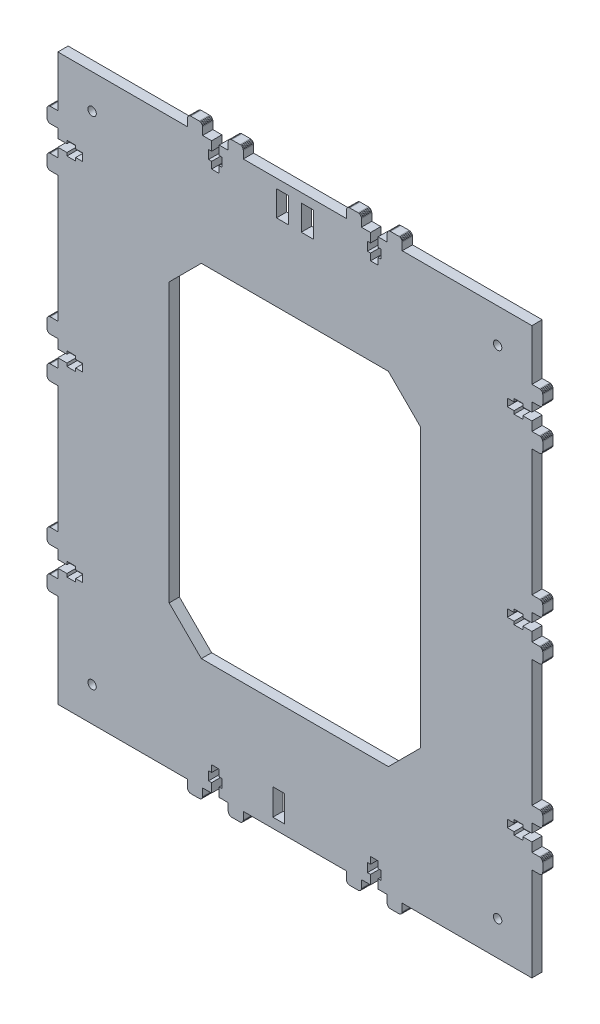
SolidWorks part; units mm, degrees
ref_plane "Plano frontal" through (0, 0, 0) normal (0, 0, 1) x (1, 0, 0)
ref_plane "Plano superior" through (0, 0, 0) normal (0, 1, 0) x (1, 0, 0)
ref_plane "Plano direito" through (0, 0, 0) normal (1, 0, 0) x (0, 0, -1)
sketch "Model" plane through (0, 0, 0) normal (0, 0, 1) x (1, 0, 0)
  line L0 (136.5926, 337.8518) -> (136.5926, 343.1518)
  line L1 (136.5926, 332.7518) -> (138.3926, 332.7518)
  line L2 (138.3926, 337.8518) -> (136.5926, 337.8518)
  line L3 (130.3926, 337.8518) -> (130.3926, 332.7518)
  line L4 (234.6925, 13.2519) -> (229.3925, 13.2519)
  line L5 (132.1926, 332.7518) -> (132.1926, 328.8018)
  line L6 (319.1925, 280.8519) -> (319.1925, 207.0019)
  line L7 (47.6926, 82.0519) -> (47.6926, 80.2519)
  line L8 (56.7426, 86.4519) -> (52.7926, 86.4519)
  line L9 (52.7926, 80.2519) -> (52.7926, 82.0519)
  line L10 (42.3926, 91.7519) -> (38.0426, 91.7519)
  line L11 (42.3926, 67.9519) -> (38.0426, 67.9519)
  line L12 (52.7926, 88.2519) -> (47.6926, 88.2519)
  line L13 (56.7426, 82.0519) -> (56.7426, 86.4519)
  line L14 (229.3925, 337.8518) -> (229.3925, 343.1518)
  line L15 (319.1925, 174.4019) -> (319.1925, 100.5519)
  line L16 (224.9925, 343.1518) -> (224.9925, 337.8518)
  line L17 (52.7926, 299.3519) -> (52.7926, 301.1519)
  line L18 (229.3925, 332.7518) -> (231.1925, 332.7518)
  line L19 (132.1926, 343.1518) -> (132.1926, 337.8518)
  line L20 (56.7426, 294.9519) -> (56.7426, 299.3519)
  line L21 (223.1925, 337.8518) -> (223.1925, 332.7518)
  line L22 (47.6926, 88.2519) -> (47.6926, 86.4519)
  line L23 (47.6926, 80.2519) -> (52.7926, 80.2519)
  line L24 (42.3926, 13.2519) -> (42.3926, 67.9519)
  line L25 (52.7926, 293.1519) -> (52.7926, 294.9519)
  line L26 (319.1925, 13.2519) -> (243.4925, 13.2519)
  line L27 (52.7926, 188.5019) -> (56.7426, 188.5019)
  line L28 (56.7426, 192.9019) -> (52.7926, 192.9019)
  line L29 (313.8925, 301.1519) -> (308.7925, 301.1519)
  line L30 (313.8925, 299.3519) -> (313.8925, 301.1519)
  line L31 (304.8425, 294.9519) -> (308.7925, 294.9519)
  line L32 (47.6926, 293.1519) -> (52.7926, 293.1519)
  line L33 (138.3926, 18.5519) -> (138.3926, 23.6519)
  line L34 (136.5926, 18.5519) -> (138.3926, 18.5519)
  line L35 (132.1926, 27.6019) -> (132.1926, 23.6519)
  line L36 (138.3926, 23.6519) -> (136.5926, 23.6519)
  line L37 (126.8926, 13.2519) -> (126.8926, 8.902)
  line L38 (150.6926, 13.2519) -> (150.6926, 8.902)
  line L39 (130.3926, 23.6519) -> (130.3926, 18.5519)
  line L40 (42.3926, 198.2019) -> (38.0426, 198.2019)
  line L41 (319.1925, 67.9519) -> (319.1925, 13.2519)
  line L42 (132.1926, 18.5519) -> (132.1926, 13.2519)
  line L43 (132.1926, 23.6519) -> (130.3926, 23.6519)
  line L44 (130.3926, 18.5519) -> (132.1926, 18.5519)
  line L45 (42.3926, 313.4519) -> (42.3926, 343.1518)
  line L46 (42.3926, 188.5019) -> (47.6926, 188.5019)
  line L47 (47.6926, 192.9019) -> (42.3926, 192.9019)
  line L48 (47.6926, 186.7019) -> (52.7926, 186.7019)
  line L49 (231.1925, 18.5519) -> (231.1925, 23.6519)
  line L50 (229.3925, 18.5519) -> (231.1925, 18.5519)
  line L51 (224.9925, 27.6019) -> (224.9925, 23.6519)
  line L52 (308.7925, 301.1519) -> (308.7925, 299.3519)
  line L53 (319.1925, 289.6519) -> (323.5425, 289.6519)
  line L54 (319.1925, 313.4518) -> (323.5425, 313.4518)
  line L55 (308.7925, 293.1519) -> (313.8925, 293.1519)
  line L56 (304.8425, 299.3519) -> (304.8425, 294.9519)
  line L57 (304.8425, 82.0519) -> (308.7925, 82.0519)
  line L58 (304.8425, 192.9019) -> (304.8425, 188.5019)
  line L59 (118.0926, 13.2519) -> (42.3926, 13.2519)
  line L60 (319.1925, 192.9019) -> (313.8925, 192.9019)
  line L61 (319.1925, 294.9519) -> (319.1925, 289.6519)
  line L62 (319.1925, 304.6519) -> (319.1925, 299.3519)
  line L63 (308.7925, 294.9519) -> (308.7925, 293.1519)
  line L64 (313.8925, 293.1519) -> (313.8925, 294.9519)
  line L65 (308.7925, 192.9019) -> (304.8425, 192.9019)
  line L66 (319.1925, 198.2019) -> (319.1925, 192.9019)
  line L67 (231.1925, 337.8518) -> (229.3925, 337.8518)
  line L68 (313.8925, 82.0519) -> (319.1925, 82.0519)
  line L69 (308.7925, 82.0519) -> (308.7925, 80.2519)
  line L70 (210.8925, 343.1518) -> (210.8925, 347.5018)
  line L71 (231.1925, 332.7518) -> (231.1925, 337.8518)
  line L72 (224.9925, 337.8518) -> (223.1925, 337.8518)
  line L73 (47.6926, 86.4519) -> (42.3926, 86.4519)
  line L74 (52.7926, 86.4519) -> (52.7926, 88.2519)
  line L75 (319.1925, 76.7519) -> (323.5425, 76.7519)
  line L76 (319.1925, 100.5519) -> (323.5425, 100.5519)
  line L77 (308.7925, 80.2519) -> (313.8925, 80.2519)
  line L78 (52.7926, 301.1519) -> (47.6926, 301.1519)
  line L79 (229.3925, 13.2519) -> (229.3925, 18.5519)
  line L80 (42.3926, 192.9019) -> (42.3926, 198.2019)
  line L81 (52.7926, 186.7019) -> (52.7926, 188.5019)
  line L82 (47.6926, 188.5019) -> (47.6926, 186.7019)
  line L83 (42.3926, 82.0519) -> (47.6926, 82.0519)
  line L84 (52.7926, 82.0519) -> (56.7426, 82.0519)
  line L85 (313.8925, 188.5019) -> (319.1925, 188.5019)
  line L86 (308.7925, 188.5019) -> (308.7925, 186.7019)
  line L87 (313.8925, 186.7019) -> (313.8925, 188.5019)
  line L88 (313.8925, 194.7019) -> (308.7925, 194.7019)
  line L89 (132.1926, 13.2519) -> (126.8926, 13.2519)
  line L90 (224.9925, 13.2519) -> (219.6925, 13.2519)
  line L91 (47.6926, 294.9519) -> (47.6926, 293.1519)
  line L92 (231.1925, 23.6519) -> (229.3925, 23.6519)
  line L93 (136.5926, 13.2519) -> (136.5926, 18.5519)
  line L94 (136.5926, 23.6519) -> (136.5926, 27.6019)
  line L95 (141.8926, 13.2519) -> (136.5926, 13.2519)
  line L96 (56.7426, 188.5019) -> (56.7426, 192.9019)
  line L97 (47.6926, 194.7019) -> (47.6926, 192.9019)
  line L98 (52.7926, 194.7019) -> (47.6926, 194.7019)
  line L99 (319.1925, 82.0519) -> (319.1925, 76.7519)
  line L100 (313.8925, 88.2519) -> (308.7925, 88.2519)
  line L101 (132.1926, 337.8518) -> (130.3926, 337.8518)
  line L102 (136.5926, 328.8018) -> (136.5926, 332.7518)
  line L103 (130.3926, 332.7518) -> (132.1926, 332.7518)
  line L104 (141.8926, 343.1518) -> (141.8926, 347.5018)
  line L105 (229.3925, 343.1518) -> (234.6925, 343.1518)
  line L106 (136.5926, 27.6019) -> (132.1926, 27.6019)
  line L107 (42.3926, 294.9519) -> (47.6926, 294.9519)
  line L108 (52.7926, 294.9519) -> (56.7426, 294.9519)
  line L109 (56.7426, 299.3519) -> (52.7926, 299.3519)
  line L110 (42.3926, 86.4519) -> (42.3926, 91.7519)
  line L111 (42.3926, 100.5519) -> (42.3926, 174.4019)
  line L112 (42.3926, 207.0019) -> (42.3926, 280.8519)
  line L113 (42.3926, 76.7519) -> (42.3926, 82.0519)
  line L114 (223.1925, 23.6519) -> (223.1925, 18.5519)
  line L115 (229.3925, 27.6019) -> (224.9925, 27.6019)
  line L116 (224.9925, 18.5519) -> (224.9925, 13.2519)
  line L117 (304.8425, 188.5019) -> (308.7925, 188.5019)
  line L118 (308.7925, 194.7019) -> (308.7925, 192.9019)
  line L119 (319.1925, 183.2019) -> (323.5425, 183.2019)
  line L120 (319.1925, 207.0019) -> (323.5425, 207.0019)
  line L121 (308.7925, 186.7019) -> (313.8925, 186.7019)
  line L122 (138.3926, 332.7518) -> (138.3926, 337.8518)
  line L123 (132.1926, 328.8018) -> (136.5926, 328.8018)
  line L124 (219.6925, 13.2519) -> (219.6925, 8.902)
  line L125 (243.4925, 13.2519) -> (243.4925, 8.902)
  line L126 (229.3925, 328.8018) -> (229.3925, 332.7518)
  line L127 (234.6925, 343.1518) -> (234.6925, 347.5018)
  line L128 (42.3926, 183.2019) -> (42.3926, 188.5019)
  line L129 (319.1925, 299.3519) -> (313.8925, 299.3519)
  line L130 (308.7925, 299.3519) -> (304.8425, 299.3519)
  line L131 (319.1925, 188.5019) -> (319.1925, 183.2019)
  line L132 (313.8925, 294.9519) -> (319.1925, 294.9519)
  line L133 (52.7926, 192.9019) -> (52.7926, 194.7019)
  line L134 (319.1925, 91.7519) -> (319.1925, 86.4519)
  line L135 (229.3925, 23.6519) -> (229.3925, 27.6019)
  line L136 (136.5926, 343.1518) -> (141.8926, 343.1518)
  line L137 (150.6926, 343.1518) -> (210.8925, 343.1518)
  line L138 (219.6925, 343.1518) -> (224.9925, 343.1518)
  line L139 (42.3926, 174.4019) -> (38.0426, 174.4019)
  line L140 (223.1925, 18.5519) -> (224.9925, 18.5519)
  line L141 (47.6926, 301.1519) -> (47.6926, 299.3519)
  line L142 (47.6926, 299.3519) -> (42.3926, 299.3519)
  line L143 (42.3926, 299.3519) -> (42.3926, 304.6519)
  line L144 (210.8925, 13.2519) -> (150.6926, 13.2519)
  line L145 (42.3926, 304.6519) -> (38.0426, 304.6519)
  line L146 (243.4925, 343.1518) -> (319.1925, 343.1518)
  line L147 (319.1925, 343.1518) -> (319.1925, 313.4518)
  line L148 (223.1925, 332.7518) -> (224.9925, 332.7518)
  line L149 (224.9925, 332.7518) -> (224.9925, 328.8018)
  line L150 (224.9925, 328.8018) -> (229.3925, 328.8018)
  line L151 (319.1925, 86.4519) -> (313.8925, 86.4519)
  line L152 (313.8925, 86.4519) -> (313.8925, 88.2519)
  line L153 (308.7925, 88.2519) -> (308.7925, 86.4519)
  line L154 (308.7925, 86.4519) -> (304.8425, 86.4519)
  line L155 (304.8425, 86.4519) -> (304.8425, 82.0519)
  line L156 (224.9925, 23.6519) -> (223.1925, 23.6519)
  line L157 (42.3926, 343.1518) -> (118.0926, 343.1518)
  line L158 (118.0926, 343.1518) -> (118.0926, 347.5018)
  line L159 (124.8926, 349.5018) -> (125.4102, 349.4337)
  line L160 (125.4102, 349.4337) -> (125.8926, 349.2339)
  line L161 (125.8926, 349.2339) -> (126.3068, 348.9161)
  line L162 (126.3068, 348.9161) -> (126.6246, 348.5018)
  line L163 (126.6246, 348.5018) -> (126.8244, 348.0195)
  line L164 (126.8926, 347.5018) -> (126.8926, 343.1518)
  line L165 (126.8244, 348.0195) -> (126.8926, 347.5018)
  line L166 (141.8926, 347.5018) -> (141.9607, 348.0195)
  line L167 (141.9607, 348.0195) -> (142.1605, 348.5018)
  line L168 (142.1605, 348.5018) -> (142.4783, 348.9161)
  line L169 (142.4783, 348.9161) -> (142.8926, 349.2339)
  line L170 (142.8926, 349.2339) -> (143.3749, 349.4337)
  line L171 (143.8926, 349.5018) -> (148.6926, 349.5018)
  line L172 (143.3749, 349.4337) -> (143.8926, 349.5018)
  line L173 (150.6926, 347.5018) -> (150.6926, 343.1518)
  line L174 (150.6926, 347.5018) -> (150.6244, 348.0195)
  line L175 (150.6244, 348.0195) -> (150.4246, 348.5018)
  line L176 (150.4246, 348.5018) -> (150.1068, 348.9161)
  line L177 (150.1068, 348.9161) -> (149.6926, 349.2339)
  line L178 (149.6926, 349.2339) -> (149.2102, 349.4337)
  line L179 (149.2102, 349.4337) -> (148.6926, 349.5018)
  line L180 (118.0926, 347.5018) -> (118.1607, 348.0195)
  line L181 (118.1607, 348.0195) -> (118.3605, 348.5018)
  line L182 (118.3605, 348.5018) -> (118.6784, 348.9161)
  line L183 (118.6784, 348.9161) -> (119.0926, 349.2339)
  line L184 (119.0926, 349.2339) -> (119.5749, 349.4337)
  line L185 (120.0926, 349.5018) -> (124.8926, 349.5018)
  line L186 (119.5749, 349.4337) -> (120.0926, 349.5018)
  line L187 (234.6925, 347.5018) -> (234.7607, 348.0195)
  line L188 (234.7607, 348.0195) -> (234.9605, 348.5018)
  line L189 (234.9605, 348.5018) -> (235.2783, 348.9161)
  line L190 (235.2783, 348.9161) -> (235.6925, 349.2339)
  line L191 (235.6925, 349.2339) -> (236.1749, 349.4337)
  line L192 (236.6925, 349.5018) -> (241.4925, 349.5018)
  line L193 (236.1749, 349.4337) -> (236.6925, 349.5018)
  line L194 (243.4925, 347.5018) -> (243.4925, 343.1518)
  line L195 (243.4925, 347.5018) -> (243.4244, 348.0195)
  line L196 (243.4244, 348.0195) -> (243.2246, 348.5018)
  line L197 (243.2246, 348.5018) -> (242.9067, 348.9161)
  line L198 (242.9067, 348.9161) -> (242.4925, 349.2339)
  line L199 (242.4925, 349.2339) -> (242.0102, 349.4337)
  line L200 (242.0102, 349.4337) -> (241.4925, 349.5018)
  line L201 (219.6925, 347.5018) -> (219.6925, 343.1518)
  line L202 (219.6925, 347.5018) -> (219.6244, 348.0195)
  line L203 (219.6244, 348.0195) -> (219.4246, 348.5018)
  line L204 (219.4246, 348.5018) -> (219.1068, 348.9161)
  line L205 (219.1068, 348.9161) -> (218.6925, 349.2339)
  line L206 (218.6925, 349.2339) -> (218.2102, 349.4337)
  line L207 (218.2102, 349.4337) -> (217.6925, 349.5018)
  line L208 (210.8925, 347.5018) -> (210.9607, 348.0195)
  line L209 (210.9607, 348.0195) -> (211.1605, 348.5018)
  line L210 (211.1605, 348.5018) -> (211.4783, 348.9161)
  line L211 (211.4783, 348.9161) -> (211.8925, 349.2339)
  line L212 (211.8925, 349.2339) -> (212.3749, 349.4337)
  line L213 (212.8925, 349.5018) -> (217.6925, 349.5018)
  line L214 (212.3749, 349.4337) -> (212.8925, 349.5018)
  line L215 (210.8925, 8.902) -> (210.8925, 13.2519)
  line L216 (210.8925, 8.902) -> (210.9607, 8.3843)
  line L217 (210.9607, 8.3843) -> (211.1605, 7.902)
  line L218 (211.1605, 7.902) -> (211.4783, 7.4877)
  line L219 (211.4783, 7.4877) -> (211.8925, 7.1699)
  line L220 (211.8925, 7.1699) -> (212.3749, 6.9701)
  line L221 (212.3749, 6.9701) -> (212.8925, 6.902)
  line L222 (219.6925, 8.902) -> (219.6244, 8.3843)
  line L223 (219.6244, 8.3843) -> (219.4246, 7.902)
  line L224 (219.4246, 7.902) -> (219.1067, 7.4877)
  line L225 (219.1067, 7.4877) -> (218.6925, 7.1699)
  line L226 (218.6925, 7.1699) -> (218.2102, 6.9701)
  line L227 (217.6925, 6.902) -> (212.8925, 6.902)
  line L228 (218.2102, 6.9701) -> (217.6925, 6.902)
  line L229 (323.5425, 174.4019) -> (319.1925, 174.4019)
  line L230 (323.5425, 174.4019) -> (324.0601, 174.47)
  line L231 (324.0601, 174.47) -> (324.5425, 174.6698)
  line L232 (324.5425, 174.6698) -> (324.9567, 174.9877)
  line L233 (324.9567, 174.9877) -> (325.2746, 175.4019)
  line L234 (325.2746, 175.4019) -> (325.4744, 175.8843)
  line L235 (325.4744, 175.8843) -> (325.5425, 176.4019)
  line L236 (325.5425, 93.7519) -> (325.4744, 93.2343)
  line L237 (325.4744, 93.2343) -> (325.2746, 92.7519)
  line L238 (325.2746, 92.7519) -> (324.9567, 92.3377)
  line L239 (324.9567, 92.3377) -> (324.5425, 92.0199)
  line L240 (324.5425, 92.0199) -> (324.0601, 91.8201)
  line L241 (323.5425, 91.7519) -> (319.1925, 91.7519)
  line L242 (324.0601, 91.8201) -> (323.5425, 91.7519)
  line L243 (36.0426, 93.7519) -> (36.0426, 98.5519)
  line L244 (36.0426, 93.7519) -> (36.1107, 93.2343)
  line L245 (36.1107, 93.2343) -> (36.3105, 92.7519)
  line L246 (36.3105, 92.7519) -> (36.6284, 92.3377)
  line L247 (36.6284, 92.3377) -> (37.0426, 92.0199)
  line L248 (37.0426, 92.0199) -> (37.525, 91.8201)
  line L249 (37.525, 91.8201) -> (38.0426, 91.7519)
  line L250 (38.0426, 67.9519) -> (37.525, 68.0201)
  line L251 (37.525, 68.0201) -> (37.0426, 68.2199)
  line L252 (37.0426, 68.2199) -> (36.6284, 68.5377)
  line L253 (36.6284, 68.5377) -> (36.3105, 68.9519)
  line L254 (36.3105, 68.9519) -> (36.1107, 69.4343)
  line L255 (36.0426, 69.9519) -> (36.0426, 74.7519)
  line L256 (36.1107, 69.4343) -> (36.0426, 69.9519)
  line L257 (38.0426, 76.7519) -> (42.3926, 76.7519)
  line L258 (38.0426, 76.7519) -> (37.525, 76.6838)
  line L259 (37.525, 76.6838) -> (37.0426, 76.484)
  line L260 (37.0426, 76.484) -> (36.6284, 76.1661)
  line L261 (36.6284, 76.1661) -> (36.3105, 75.7519)
  line L262 (36.3105, 75.7519) -> (36.1107, 75.2696)
  line L263 (36.1107, 75.2696) -> (36.0426, 74.7519)
  line L264 (36.0426, 306.6519) -> (36.0426, 311.4519)
  line L265 (36.0426, 306.6519) -> (36.1107, 306.1342)
  line L266 (36.1107, 306.1342) -> (36.3105, 305.6519)
  line L267 (36.3105, 305.6519) -> (36.6284, 305.2376)
  line L268 (36.6284, 305.2376) -> (37.0426, 304.9198)
  line L269 (37.0426, 304.9198) -> (37.525, 304.72)
  line L270 (37.525, 304.72) -> (38.0426, 304.6519)
  line L271 (325.5425, 69.9519) -> (325.4744, 69.4343)
  line L272 (325.4744, 69.4343) -> (325.2746, 68.9519)
  line L273 (325.2746, 68.9519) -> (324.9567, 68.5377)
  line L274 (324.9567, 68.5377) -> (324.5425, 68.2199)
  line L275 (324.5425, 68.2199) -> (324.0601, 68.0201)
  line L276 (323.5425, 67.9519) -> (319.1925, 67.9519)
  line L277 (324.0601, 68.0201) -> (323.5425, 67.9519)
  line L278 (124.8926, 6.902) -> (120.0926, 6.902)
  line L279 (124.8926, 6.902) -> (125.4102, 6.9701)
  line L280 (125.4102, 6.9701) -> (125.8926, 7.1699)
  line L281 (125.8926, 7.1699) -> (126.3068, 7.4877)
  line L282 (126.3068, 7.4877) -> (126.6246, 7.902)
  line L283 (126.6246, 7.902) -> (126.8244, 8.3843)
  line L284 (126.8244, 8.3843) -> (126.8926, 8.902)
  line L285 (118.0926, 8.902) -> (118.0926, 13.2519)
  line L286 (118.0926, 8.902) -> (118.1607, 8.3843)
  line L287 (118.1607, 8.3843) -> (118.3605, 7.902)
  line L288 (118.3605, 7.902) -> (118.6784, 7.4877)
  line L289 (118.6784, 7.4877) -> (119.0926, 7.1699)
  line L290 (119.0926, 7.1699) -> (119.5749, 6.9701)
  line L291 (119.5749, 6.9701) -> (120.0926, 6.902)
  line L292 (38.0426, 100.5519) -> (42.3926, 100.5519)
  line L293 (38.0426, 100.5519) -> (37.525, 100.4838)
  line L294 (37.525, 100.4838) -> (37.0426, 100.284)
  line L295 (37.0426, 100.284) -> (36.6284, 99.9661)
  line L296 (36.6284, 99.9661) -> (36.3105, 99.5519)
  line L297 (36.3105, 99.5519) -> (36.1107, 99.0696)
  line L298 (36.1107, 99.0696) -> (36.0426, 98.5519)
  line L299 (323.5425, 304.6519) -> (319.1925, 304.6519)
  line L300 (323.5425, 304.6519) -> (324.0601, 304.72)
  line L301 (324.0601, 304.72) -> (324.5425, 304.9198)
  line L302 (324.5425, 304.9198) -> (324.9567, 305.2376)
  line L303 (324.9567, 305.2376) -> (325.2746, 305.6519)
  line L304 (325.2746, 305.6519) -> (325.4744, 306.1342)
  line L305 (325.4744, 306.1342) -> (325.5425, 306.6519)
  line L306 (325.5425, 287.6519) -> (325.5425, 282.8519)
  line L307 (325.5425, 287.6519) -> (325.4744, 288.1695)
  line L308 (325.4744, 288.1695) -> (325.2746, 288.6519)
  line L309 (325.2746, 288.6519) -> (324.9567, 289.0661)
  line L310 (324.9567, 289.0661) -> (324.5425, 289.3839)
  line L311 (324.5425, 289.3839) -> (324.0601, 289.5837)
  line L312 (324.0601, 289.5837) -> (323.5425, 289.6519)
  line L313 (323.5425, 280.8519) -> (319.1925, 280.8519)
  line L314 (323.5425, 280.8519) -> (324.0601, 280.92)
  line L315 (324.0601, 280.92) -> (324.5425, 281.1198)
  line L316 (324.5425, 281.1198) -> (324.9567, 281.4377)
  line L317 (324.9567, 281.4377) -> (325.2746, 281.8519)
  line L318 (325.2746, 281.8519) -> (325.4744, 282.3342)
  line L319 (325.4744, 282.3342) -> (325.5425, 282.8519)
  line L320 (148.6926, 6.902) -> (143.8926, 6.902)
  line L321 (148.6926, 6.902) -> (149.2102, 6.9701)
  line L322 (149.2102, 6.9701) -> (149.6926, 7.1699)
  line L323 (149.6926, 7.1699) -> (150.1068, 7.4877)
  line L324 (150.1068, 7.4877) -> (150.4246, 7.902)
  line L325 (150.4246, 7.902) -> (150.6244, 8.3843)
  line L326 (150.6244, 8.3843) -> (150.6926, 8.902)
  line L327 (36.0426, 200.2019) -> (36.0426, 205.0019)
  line L328 (36.0426, 200.2019) -> (36.1107, 199.6843)
  line L329 (36.1107, 199.6843) -> (36.3105, 199.2019)
  line L330 (36.3105, 199.2019) -> (36.6284, 198.7877)
  line L331 (36.6284, 198.7877) -> (37.0426, 198.4698)
  line L332 (37.0426, 198.4698) -> (37.525, 198.27)
  line L333 (37.525, 198.27) -> (38.0426, 198.2019)
  line L334 (141.8926, 8.902) -> (141.8926, 13.2519)
  line L335 (141.8926, 8.902) -> (141.9607, 8.3843)
  line L336 (141.9607, 8.3843) -> (142.1605, 7.902)
  line L337 (142.1605, 7.902) -> (142.4783, 7.4877)
  line L338 (142.4783, 7.4877) -> (142.8926, 7.1699)
  line L339 (142.8926, 7.1699) -> (143.3749, 6.9701)
  line L340 (143.3749, 6.9701) -> (143.8926, 6.902)
  line L341 (38.0426, 207.0019) -> (42.3926, 207.0019)
  line L342 (38.0426, 207.0019) -> (37.525, 206.9337)
  line L343 (37.525, 206.9337) -> (37.0426, 206.7339)
  line L344 (37.0426, 206.7339) -> (36.6284, 206.4161)
  line L345 (36.6284, 206.4161) -> (36.3105, 206.0019)
  line L346 (36.3105, 206.0019) -> (36.1107, 205.5195)
  line L347 (36.1107, 205.5195) -> (36.0426, 205.0019)
  line L348 (38.0426, 313.4519) -> (42.3926, 313.4519)
  line L349 (38.0426, 313.4519) -> (37.525, 313.3837)
  line L350 (37.525, 313.3837) -> (37.0426, 313.1839)
  line L351 (37.0426, 313.1839) -> (36.6284, 312.8661)
  line L352 (36.6284, 312.8661) -> (36.3105, 312.4519)
  line L353 (36.3105, 312.4519) -> (36.1107, 311.9695)
  line L354 (36.1107, 311.9695) -> (36.0426, 311.4519)
  line L355 (38.0426, 289.6519) -> (42.3926, 289.6519)
  line L356 (38.0426, 289.6519) -> (37.525, 289.5837)
  line L357 (37.525, 289.5837) -> (37.0426, 289.3839)
  line L358 (37.0426, 289.3839) -> (36.6284, 289.0661)
  line L359 (36.6284, 289.0661) -> (36.3105, 288.6519)
  line L360 (36.3105, 288.6519) -> (36.1107, 288.1695)
  line L361 (36.1107, 288.1695) -> (36.0426, 287.6519)
  line L362 (323.5425, 313.4518) -> (324.0601, 313.3837)
  line L363 (324.0601, 313.3837) -> (324.5425, 313.1839)
  line L364 (324.5425, 313.1839) -> (324.9567, 312.8661)
  line L365 (324.9567, 312.8661) -> (325.2746, 312.4518)
  line L366 (325.2746, 312.4518) -> (325.4744, 311.9695)
  line L367 (325.5425, 311.4518) -> (325.5425, 306.6519)
  line L368 (325.4744, 311.9695) -> (325.5425, 311.4518)
  line L369 (236.6925, 6.902) -> (236.1749, 6.9701)
  line L370 (236.1749, 6.9701) -> (235.6925, 7.1699)
  line L371 (235.6925, 7.1699) -> (235.2783, 7.4877)
  line L372 (235.2783, 7.4877) -> (234.9605, 7.902)
  line L373 (234.9605, 7.902) -> (234.7607, 8.3843)
  line L374 (234.6925, 8.902) -> (234.6925, 13.2519)
  line L375 (234.7607, 8.3843) -> (234.6925, 8.902)
  line L376 (325.5425, 74.7519) -> (325.5425, 69.9519)
  line L377 (325.5425, 74.7519) -> (325.4744, 75.2696)
  line L378 (325.4744, 75.2696) -> (325.2746, 75.7519)
  line L379 (325.2746, 75.7519) -> (324.9567, 76.1661)
  line L380 (324.9567, 76.1661) -> (324.5425, 76.484)
  line L381 (324.5425, 76.484) -> (324.0601, 76.6838)
  line L382 (324.0601, 76.6838) -> (323.5425, 76.7519)
  line L383 (323.5425, 100.5519) -> (324.0601, 100.4838)
  line L384 (324.0601, 100.4838) -> (324.5425, 100.284)
  line L385 (324.5425, 100.284) -> (324.9567, 99.9661)
  line L386 (324.9567, 99.9661) -> (325.2746, 99.5519)
  line L387 (325.2746, 99.5519) -> (325.4744, 99.0696)
  line L388 (325.5425, 98.5519) -> (325.5425, 93.7519)
  line L389 (325.4744, 99.0696) -> (325.5425, 98.5519)
  line L390 (325.5425, 200.2019) -> (325.4744, 199.6842)
  line L391 (325.4744, 199.6842) -> (325.2746, 199.2019)
  line L392 (325.2746, 199.2019) -> (324.9567, 198.7877)
  line L393 (324.9567, 198.7877) -> (324.5425, 198.4698)
  line L394 (324.5425, 198.4698) -> (324.0601, 198.27)
  line L395 (323.5425, 198.2019) -> (319.1925, 198.2019)
  line L396 (324.0601, 198.27) -> (323.5425, 198.2019)
  line L397 (323.5425, 183.2019) -> (324.0601, 183.1337)
  line L398 (324.0601, 183.1337) -> (324.5425, 182.9339)
  line L399 (324.5425, 182.9339) -> (324.9567, 182.6161)
  line L400 (324.9567, 182.6161) -> (325.2746, 182.2019)
  line L401 (325.2746, 182.2019) -> (325.4744, 181.7195)
  line L402 (325.5425, 181.2019) -> (325.5425, 176.4019)
  line L403 (325.4744, 181.7195) -> (325.5425, 181.2019)
  line L404 (38.0426, 183.2019) -> (42.3926, 183.2019)
  line L405 (38.0426, 183.2019) -> (37.525, 183.1338)
  line L406 (37.525, 183.1338) -> (37.0426, 182.9339)
  line L407 (37.0426, 182.9339) -> (36.6284, 182.6161)
  line L408 (36.6284, 182.6161) -> (36.3105, 182.2019)
  line L409 (36.3105, 182.2019) -> (36.1107, 181.7195)
  line L410 (36.1107, 181.7195) -> (36.0426, 181.2019)
  line L411 (241.4925, 6.902) -> (236.6925, 6.902)
  line L412 (241.4925, 6.902) -> (242.0102, 6.9701)
  line L413 (242.0102, 6.9701) -> (242.4925, 7.1699)
  line L414 (242.4925, 7.1699) -> (242.9067, 7.4877)
  line L415 (242.9067, 7.4877) -> (243.2246, 7.902)
  line L416 (243.2246, 7.902) -> (243.4244, 8.3843)
  line L417 (243.4244, 8.3843) -> (243.4925, 8.902)
  line L418 (323.5425, 207.0019) -> (324.0601, 206.9337)
  line L419 (324.0601, 206.9337) -> (324.5425, 206.7339)
  line L420 (324.5425, 206.7339) -> (324.9567, 206.4161)
  line L421 (324.9567, 206.4161) -> (325.2746, 206.0019)
  line L422 (325.2746, 206.0019) -> (325.4744, 205.5195)
  line L423 (325.5425, 205.0019) -> (325.5425, 200.2019)
  line L424 (325.4744, 205.5195) -> (325.5425, 205.0019)
  line L425 (36.0426, 176.4019) -> (36.0426, 181.2019)
  line L426 (36.0426, 176.4019) -> (36.1107, 175.8843)
  line L427 (36.1107, 175.8843) -> (36.3105, 175.4019)
  line L428 (36.3105, 175.4019) -> (36.6284, 174.9877)
  line L429 (36.6284, 174.9877) -> (37.0426, 174.6699)
  line L430 (37.0426, 174.6699) -> (37.525, 174.4701)
  line L431 (37.525, 174.4701) -> (38.0426, 174.4019)
  line L432 (36.0426, 282.8519) -> (36.0426, 287.6519)
  line L433 (36.0426, 282.8519) -> (36.1107, 282.3342)
  line L434 (36.1107, 282.3342) -> (36.3105, 281.8519)
  line L435 (36.3105, 281.8519) -> (36.6284, 281.4377)
  line L436 (36.6284, 281.4377) -> (37.0426, 281.1198)
  line L437 (37.0426, 281.1198) -> (37.525, 280.92)
  line L438 (37.525, 280.92) -> (38.0426, 280.8519)
  line L439 (42.3926, 280.8519) -> (38.0426, 280.8519)
  line L440 (313.8925, 192.9019) -> (313.8925, 194.7019)
  line L441 (42.3926, 289.6519) -> (42.3926, 294.9519)
  line L442 (126.8926, 343.1518) -> (132.1926, 343.1518)
  line L443 (313.8925, 80.2519) -> (313.8925, 82.0519)
  line L444 (191.5425, 323.0519) -> (184.5425, 323.0519)
  line L445 (184.5425, 323.0519) -> (184.5425, 337.8518)
  line L446 (184.5425, 337.8518) -> (191.5425, 337.8518)
  line L447 (191.5425, 337.8518) -> (191.5425, 323.0519)
  line L448 (170.0426, 337.8518) -> (177.0425, 337.8518)
  line L449 (177.0425, 337.8518) -> (177.0425, 323.0519)
  line L450 (177.0425, 323.0519) -> (170.0426, 323.0519)
  line L451 (170.0426, 323.0519) -> (170.0426, 337.8518)
  line L452 (167.9426, 18.9519) -> (167.9426, 34.3519)
  line L453 (167.9426, 34.3519) -> (174.8425, 34.3519)
  line L454 (174.8425, 34.3519) -> (174.8425, 18.9519)
  line L455 (174.8425, 18.9519) -> (167.9426, 18.9519)
  line L456 (254.1925, 97.0387) -> (254.1925, 259.365)
  line L457 (254.1925, 259.365) -> (235.4057, 278.1518)
  line L458 (235.4057, 278.1518) -> (126.1794, 278.1518)
  line L459 (126.1794, 278.1518) -> (107.3926, 259.365)
  line L460 (107.3926, 259.365) -> (107.3926, 97.0387)
  line L461 (107.3926, 97.0387) -> (126.1794, 78.2519)
  line L462 (126.1794, 78.2519) -> (235.4057, 78.2519)
  line L463 (235.4057, 78.2519) -> (254.1925, 97.0387)
  circle A0 centre (299.1925, 323.1518) radius 2.45
  circle A1 centre (299.1925, 33.2519) radius 2.45
  circle A2 centre (62.3926, 33.2519) radius 2.45
  circle A3 centre (62.3926, 323.1518) radius 2.45
extrude "Ressalto-extrusão1" add sketch "Model" along normal blind 6
ref_plane "Plano1" through (0, 26.6519, 0) normal (0, 1, 0) x (1, 0, 0)
ref_plane "Plano2" through (0, 330.4518, 0) normal (0, -1, 0) x (-1, 0, 0)
